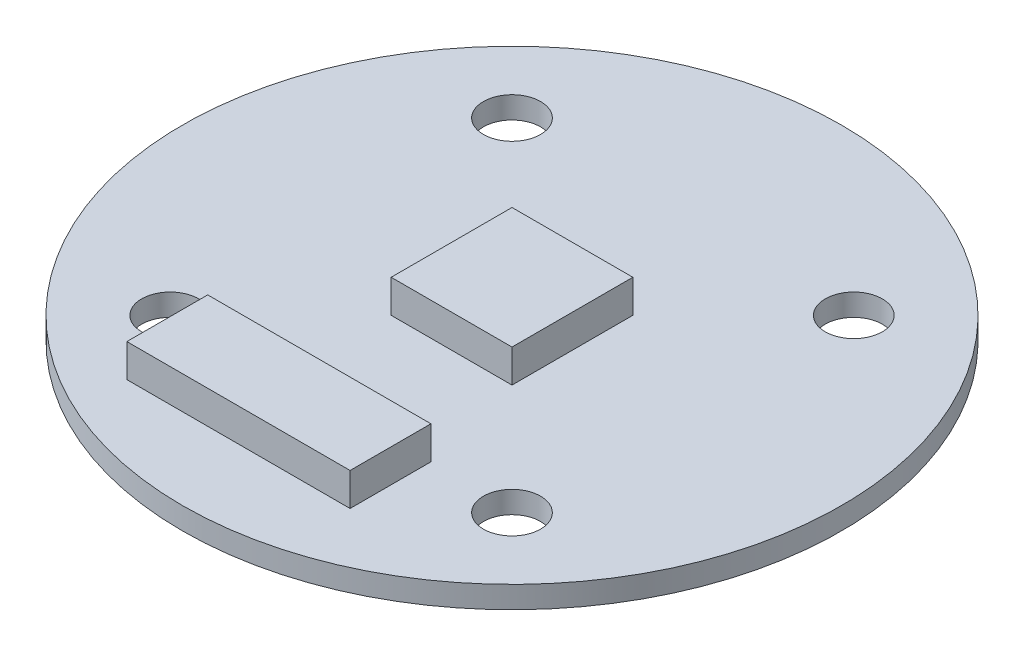
SolidWorks part; units mm, degrees
ref_plane "前视基准面" through (0, 0, 0) normal (0, 0, 1) x (1, 0, 0)
ref_plane "上视基准面" through (0, 0, 0) normal (0, 1, 0) x (1, 0, 0)
ref_plane "右视基准面" through (0, 0, 0) normal (1, 0, 0) x (0, 0, -1)
sketch "草图1" plane through (0, 0, 0) normal (0, 1, 0) x (1, 0, 0)
  line L0 (-5.4786, 0) -> (0, 0) construction
  line L1 (0, 0) -> (-7.7782, 7.7782)
  circle A0 centre (0, 0) radius 15
  circle A5 centre (-7.7782, 7.7782) radius 1.3
  circle A6 centre (7.7782, 7.7782) radius 1.3
  circle A7 centre (7.7782, -7.7782) radius 1.3
  circle A8 centre (-7.7782, -7.7782) radius 1.3
  point P14 (0, 0)
  point P16 (0, 0)
  dimension "D1" = 30
  dimension "D2" = 2.6
  dimension "D3" = 11
  dimension "D5" = 45
  dimension "D9" = 4
extrude "凸台-拉伸2" add sketch "草图1" along normal blind 1
sketch "草图2" plane through (0, 1, 0) normal (0, 1, 0) x (1, 0, 0)
  line L1 (-3.4, 16.33) -> (3.4, 16.33)
  line L2 (-3.4, 16.33) -> (-3.4, 12.13)
  line L3 (-3.4, 12.13) -> (3.4, 12.13)
  line L4 (3.4, 16.33) -> (3.4, 12.13)
  line L5 (2.75, -2.75) -> (-2.75, -2.75)
  line L6 (2.75, -2.75) -> (2.75, 2.75)
  line L7 (2.75, 2.75) -> (-2.75, 2.75)
  line L8 (-2.75, -2.75) -> (-2.75, 2.75)
  line L9 (2.75, -2.75) -> (-2.75, 2.75) construction
  line L10 (2.75, 2.75) -> (-2.75, -2.75) construction
  line L11 (-6.23, -7.62) -> (3.93, -7.62)
  line L12 (-6.23, -7.62) -> (-6.23, -11.3)
  line L13 (-6.23, -11.3) -> (3.93, -11.3)
  line L14 (3.93, -7.62) -> (3.93, -11.3)
  point P4 (0, 0)
  dimension "D1" = 4.2
  dimension "D2" = 6.8
  dimension "D3" = 12.13
  dimension "D4" = 3.4
  dimension "D5" = 5.5
  dimension "D6" = 3.68
  dimension "D7" = 10.16
  dimension "D8" = 7.62
  dimension "D9" = 3.93
extrude "凸台-拉伸5" add sketch "草图2" along normal blind 1.5 contours L8 L5 L6 L7 | L14 L11 L12 L13
sketch "草图3" plane through (0, 0, 0) normal (0, -1, 0) x (1, 0, 0)
  line L5 (-12.24, -2.67) -> (-16.64, -2.67)
  line L6 (-12.24, -2.67) -> (-12.24, 2.67)
  line L7 (-12.24, 2.67) -> (-16.64, 2.67)
  line L8 (-16.64, -2.67) -> (-16.64, 2.67)
  line L9 (2.5, -1.685) -> (-2.5, -1.685)
  line L10 (2.5, -1.685) -> (2.5, 1.685)
  line L11 (2.5, 1.685) -> (-2.5, 1.685)
  line L12 (-2.5, -1.685) -> (-2.5, 1.685)
  line L13 (2.5, -1.685) -> (-2.5, 1.685) construction
  line L14 (2.5, 1.685) -> (-2.5, -1.685) construction
  point P8 (0, 0)
  dimension "D1" = 5
  dimension "D2" = 3.37
  dimension "D3" = 4.4
  dimension "D4" = 5.34
  dimension "D5" = 12.24
  dimension "D6" = 2.67
extrude "凸台-拉伸7" add sketch "草图3" along normal blind 1.5 contours L12 L9 L10 L11
